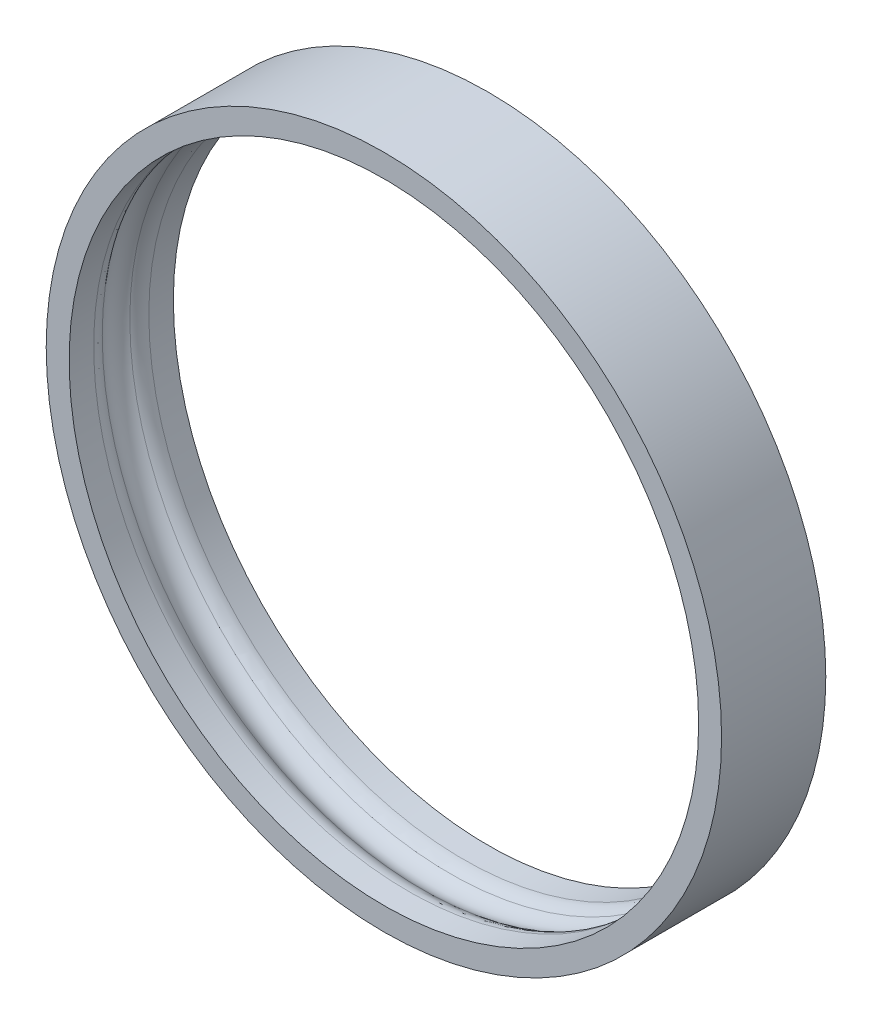
SolidWorks part; units mm, degrees
ref_plane "前视基准面" through (0, 0, 0) normal (0, 0, 1) x (1, 0, 0)
ref_plane "上视基准面" through (0, 0, 0) normal (0, 1, 0) x (1, 0, 0)
ref_plane "右视基准面" through (0, 0, 0) normal (1, 0, 0) x (0, 0, -1)
sketch "草图1" plane through (0, 0, 0) normal (0, 0, 1) x (1, 0, 0)
  circle A0 centre (0, 0) radius 15.1
  circle A1 centre (0, 0) radius 16.2
  dimension "D1" = 32.4
  dimension "D2" = 30.2
extrude "凸台-拉伸1" add sketch "草图1" along normal mid plane 5
sketch "草图3" plane through (0, 0, 0) normal (0, 1, 0) x (1, 0, 0)
  circle A0 centre (-14.6, 0) radius 1
  dimension "D1" = 2
  dimension "D2" = 14.6
revolve "切除-旋转1" cut sketch "草图3" angle 360 about axis through (0, 0, 2.5) along (0, 0, -1)
fillet "圆角1" radius 1 2 edges at (-15.1, 0, 0.866) (15.1, 0, -0.866)
equation "\"d\" = 32.4"
equation "\"D1@草图1\"=\"d\""
equation "\"d2\"= \"d\" - 2.2"
equation "\"D2@草图1\"=\"d2\""
equation "\"l1\"= \"d2\" / 2 - 0.5"
equation "\"D2@草图3\"=\"l1\""
